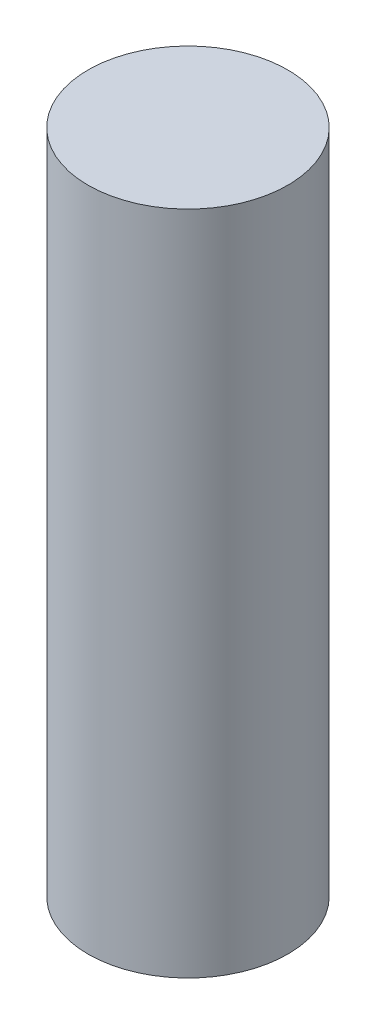
SolidWorks part; units mm, degrees
ref_plane "Front Plane" through (0, 0, 0) normal (0, 0, 1) x (1, 0, 0)
ref_plane "Top Plane" through (0, 0, 0) normal (0, 1, 0) x (1, 0, 0)
ref_plane "Right Plane" through (0, 0, 0) normal (1, 0, 0) x (0, 0, -1)
sketch "Sketch1" plane through (0, 0, 0) normal (0, 1, 0) x (1, 0, 0)
  circle A0 centre (0, 0) radius 45
  dimension "D1" = 90
extrude "Boss-Extrude1" add sketch "Sketch1" along normal blind 300
